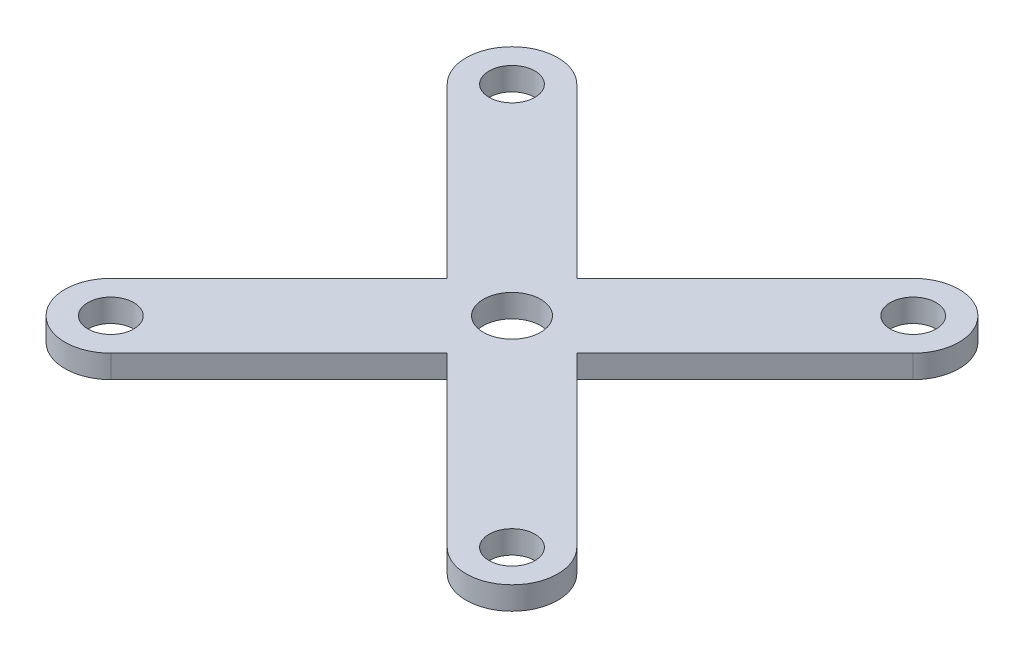
SolidWorks part; units mm, degrees
ref_plane "Front Plane" through (0, 0, 0) normal (0, 0, 1) x (1, 0, 0)
ref_plane "Top Plane" through (0, 0, 0) normal (0, 1, 0) x (1, 0, 0)
ref_plane "Right Plane" through (0, 0, 0) normal (1, 0, 0) x (0, 0, -1)
sketch "Sketch1" plane through (0, 0, 0) normal (0, 1, 0) x (1, 0, 0)
  line L0 (-17.5009, 17.5009) -> (17.5009, -17.5009) construction
  line L1 (0, 0) -> (-5.6569, 0) construction
  line L2 (17.5009, 17.5009) -> (-17.5009, -17.5009) construction
  line L3 (-20.3293, 14.6725) -> (-5.6569, 0)
  line L4 (14.6725, 20.3293) -> (0, 5.6569)
  line L5 (-14.6725, 20.3293) -> (0, 5.6569)
  line L6 (20.3293, 14.6725) -> (5.6569, 0)
  line L7 (-5.6569, 0) -> (-20.3293, -14.6725)
  line L8 (14.6725, 20.3293) -> (-20.3293, -14.6725) construction
  line L9 (5.6569, 0) -> (20.3293, -14.6725)
  line L10 (-14.6725, 20.3293) -> (20.3293, -14.6725) construction
  line L11 (0, -5.6569) -> (-14.6725, -20.3293)
  line L12 (20.3293, 14.6725) -> (-14.6725, -20.3293) construction
  line L13 (0, -5.6569) -> (14.6725, -20.3293)
  line L14 (-20.3293, 14.6725) -> (14.6725, -20.3293) construction
  circle A0 centre (-17.5009, 17.5009) radius 2
  circle A1 centre (17.5009, 17.5009) radius 2
  circle A2 centre (17.5009, -17.5009) radius 2
  circle A3 centre (-17.5009, -17.5009) radius 2
  arc A4 (-20.3293, 14.6725) -> (-14.6725, 20.3293) centre (-17.5009, 17.5009) cw
  arc A5 (20.3293, 14.6725) -> (14.6725, 20.3293) centre (17.5009, 17.5009) ccw
  arc A6 (14.6725, -20.3293) -> (20.3293, -14.6725) centre (17.5009, -17.5009) ccw
  arc A7 (-20.3293, -14.6725) -> (-14.6725, -20.3293) centre (-17.5009, -17.5009) ccw
  point P2 (0, 0)
  point P5 (0, 0)
  dimension "D4" = 4
  dimension "D1" = 49.5
  dimension "D2" = 4
  dimension "D3" = 4
extrude "Boss-Extrude1" add sketch "Sketch1" along normal blind 2 contours L7 A7 L11 L13 A6 L9 L6 A5 L4 L5 A4 L3 A0 A1 A2 A3
sketch "Sketch2" plane through (0, 2, 0) normal (0, 1, 0) x (1, 0, 0)
  circle A0 centre (0, 0) radius 2.5
  dimension "D1" = 5
extrude "Cut-Extrude1" cut sketch "Sketch2" against normal blind 2
